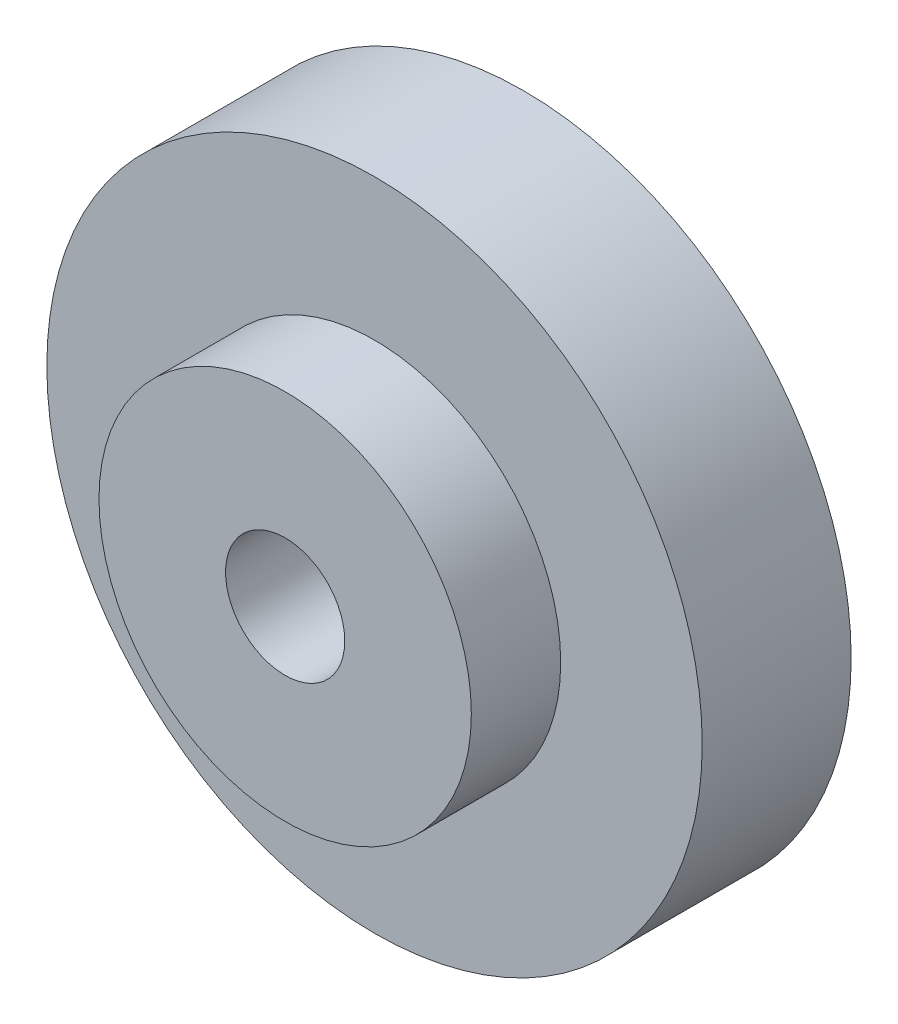
SolidWorks part; units mm, degrees
ref_plane "Front Plane" through (0, 0, 0) normal (0, 0, 1) x (1, 0, 0)
ref_plane "Top Plane" through (0, 0, 0) normal (0, 1, 0) x (1, 0, 0)
ref_plane "Right Plane" through (0, 0, 0) normal (1, 0, 0) x (0, 0, -1)
sketch "Sketch1" plane through (0, 0, 0) normal (0, 0, 1) x (1, 0, 0)
  circle A0 centre (0, 0) radius 22
  circle A1 centre (0, 0) radius 4
  dimension "D1" = 8
  dimension "D2" = 44
extrude "Boss-Extrude1" add sketch "Sketch1" along normal blind 10
sketch "Sketch2" plane through (0, 0, 10) normal (0, 0, 1) x (1, 0, 0)
  circle A0 centre (0, 0) radius 12.5
  circle A1 centre (0, 0) radius 4 construction
  circle A2 centre (0, 0) radius 4
  dimension "D1" = 25
extrude "Boss-Extrude2" add sketch "Sketch2" along normal blind 6
